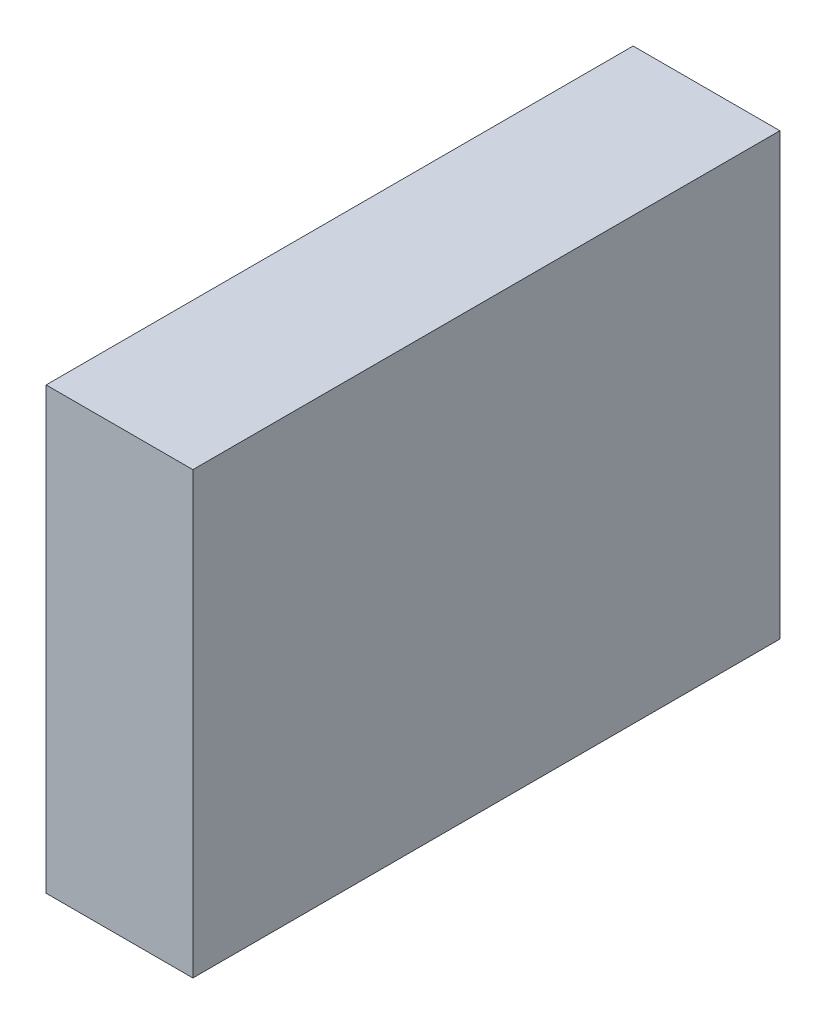
SolidWorks part; units mm, degrees
ref_plane "Front Plane" through (0, 0, 0) normal (0, 0, 1) x (1, 0, 0)
ref_plane "Top Plane" through (0, 0, 0) normal (0, 1, 0) x (1, 0, 0)
ref_plane "Right Plane" through (0, 0, 0) normal (1, 0, 0) x (0, 0, -1)
sketch "Sketch4" plane through (0, 0, 0) normal (0, 1, 0) x (1, 0, 0)
  line L1 (0, 0) -> (10, 0)
  line L2 (0, 0) -> (0, 40)
  line L3 (0, 40) -> (10, 40)
  line L4 (10, 0) -> (10, 40)
  dimension "D1" = 10
  dimension "D2" = 40
extrude "Boss-Extrude2" add sketch "Sketch4" along normal blind 30
sketch "Sketch10" plane through (0, 30, 0) normal (0, 1, 0) x (1, 0, 0)
  line L0 (10, 20) -> (0, 20)
  line L1 (10, 0) -> (10, 40) construction
  line L2 (0, 40) -> (0, 0) construction
sketch "Sketch12" plane through (0, 30, 0) normal (0, 1, 0) x (1, 0, 0)
  line L0 (10, 20) -> (34.9093, 20)
